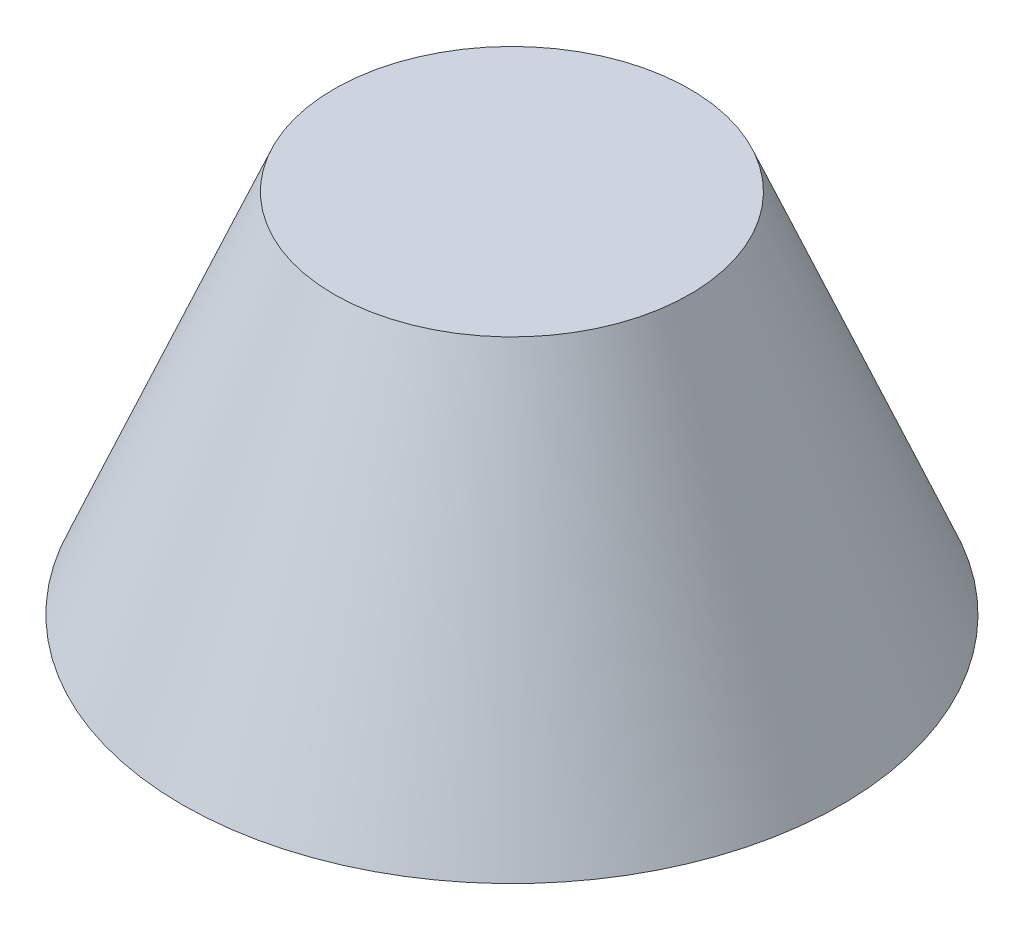
SolidWorks part; units mm, degrees
ref_plane "前视基准面" through (0, 0, 0) normal (0, 0, 1) x (1, 0, 0)
ref_plane "上视基准面" through (0, 0, 0) normal (0, 1, 0) x (1, 0, 0)
ref_plane "右视基准面" through (0, 0, 0) normal (1, 0, 0) x (0, 0, -1)
sketch "草图1" plane through (0, 0, 0) normal (0, 1, 0) x (1, 0, 0)
  circle A0 centre (0, 0) radius 90
extrude "凸台-拉伸1" add sketch "草图1" along normal blind 100 draft 22.5
